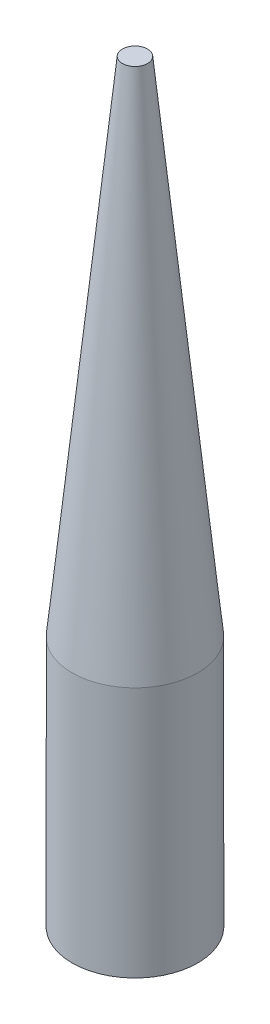
SolidWorks part; units mm, degrees
ref_plane "Front Plane" through (0, 0, 0) normal (0, 0, 1) x (1, 0, 0)
ref_plane "Top Plane" through (0, 0, 0) normal (0, 1, 0) x (1, 0, 0)
ref_plane "Right Plane" through (0, 0, 0) normal (1, 0, 0) x (0, 0, -1)
sketch "Sketch1" plane through (0, 0, 0) normal (0, 1, 0) x (1, 0, 0)
  circle A0 centre (0, 0) radius 2.5
extrude "Boss-Extrude1" add sketch "Sketch1" along normal blind 10
sketch "Sketch3" plane through (0, 0, 0) normal (0, 0, 1) x (1, 0, 0)
  line L0 (0, 10) -> (0, 30) construction
  line L1 (2.5, 10) -> (-2.5, 10) construction
  line L2 (0, 30) -> (0.5, 30)
  line L3 (0, 10) -> (2.5, 10)
  line L4 (0.5, 30) -> (2.5, 10)
  line L5 (0, 10) -> (0, 30)
revolve "Revolve1" add sketch "Sketch3" angle 360 about L0
